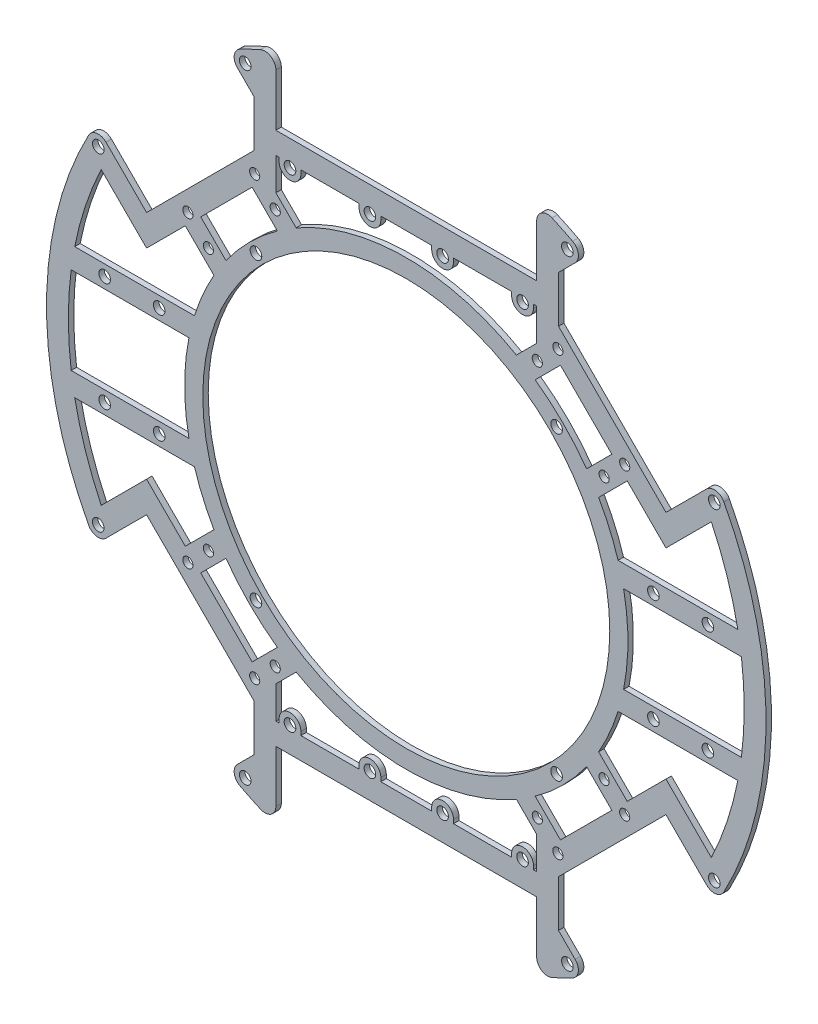
SolidWorks part; units mm, degrees
ref_plane "Front" through (0, 0, 0) normal (0, 0, 1) x (1, 0, 0)
ref_plane "Top" through (0, 0, 0) normal (0, 1, 0) x (1, 0, 0)
ref_plane "Right" through (0, 0, 0) normal (1, 0, 0) x (0, 0, -1)
sketch "Sketch1" plane through (0, 0, 0) normal (0, 0, 1) x (1, 0, 0)
  line L0 (-56.5685, 42.4264) -> (-49.621, 35.4789)
  line L4 (-35.8888, 73.4121) -> (-35.8888, 92.2659)
  line L9 (-42.4264, 56.5685) -> (-35.4789, 49.621)
  line L12 (-57.3374, 34.71) -> (-52.937, 30.3096)
  line L13 (-57.3374, 34.71) -> (-60.8112, 38.1838)
  line L16 (-41.8888, 80.4121) -> (-41.8888, 65.5914)
  line L17 (-35.8888, 67.4121) -> (-35.8888, 58.5162)
  line L19 (-41.8888, 80.4121) -> (-48.0398, 86.5631)
  line L23 (60.8112, 38.1838) -> (71.4656, 27.5293)
  line L27 (0, 67.4121) -> (-35.8888, 67.4121)
  line L28 (-53.7401, 53.7401) -> (-41.8888, 65.5914)
  line L41 (-35.8888, 58.5162) -> (-30.3096, 52.937)
  line L42 (-30.3096, 52.937) -> (-35.8888, 58.5162)
  line L45 (-53.7401, 53.7401) -> (-65.0538, 42.4264)
  line L46 (42.4264, 56.5685) -> (56.5685, 42.4264)
  line L64 (0, 0) -> (20.276, 0)
  line L79 (-42.4264, 56.5685) -> (-56.5685, 42.4264)
  line L84 (-65.0538, 42.4264) -> (-71.4656, 36.0146)
  line L85 (83.9512, 40.0149) -> (71.4656, 27.5293)
  line L90 (53.7401, 53.7401) -> (65.0538, 42.4264)
  line L91 (30.3096, 52.937) -> (35.8888, 58.5162)
  line L92 (82.6416, 47.1906) -> (71.4656, 36.0146)
  line L93 (-82.6416, 47.1906) -> (-71.4656, 36.0146)
  line L94 (-35.8888, 73.4121) -> (35.8888, 73.4121)
  line L95 (35.8888, 58.5162) -> (30.3096, 52.937)
  line L96 (53.7401, 53.7401) -> (41.8888, 65.5914)
  line L97 (41.8888, 80.4121) -> (41.8888, 65.5914)
  line L98 (0, 0) -> (0, 18.683)
  line L99 (35.8888, 67.4121) -> (35.8888, 58.5162)
  line L100 (41.8888, 80.4121) -> (48.0398, 86.5631)
  line L101 (57.3374, 34.71) -> (60.8112, 38.1838)
  line L102 (57.3374, 34.71) -> (52.937, 30.3096)
  line L104 (65.0538, 42.4264) -> (71.4656, 36.0146)
  line L105 (-83.9512, 40.0149) -> (-71.4656, 27.5293)
  line L106 (-60.8112, 38.1838) -> (-71.4656, 27.5293)
  line L107 (82.6416, -47.1906) -> (71.4656, -36.0146)
  line L108 (65.0538, -42.4264) -> (71.4656, -36.0146)
  line L109 (42.4264, 56.5685) -> (35.4789, 49.621)
  line L110 (35.8888, 73.4121) -> (35.8888, 92.2659)
  line L111 (56.5685, 42.4264) -> (49.621, 35.4789)
  line L112 (0, 67.4121) -> (35.8888, 67.4121)
  line L113 (0, -67.4121) -> (35.8888, -67.4121)
  line L114 (56.5685, -42.4264) -> (49.621, -35.4789)
  line L115 (35.8888, -73.4121) -> (35.8888, -92.2659)
  line L116 (42.4264, -56.5685) -> (35.4789, -49.621)
  line L117 (60.8112, -38.1838) -> (71.4656, -27.5293)
  line L118 (57.3374, -34.71) -> (52.937, -30.3096)
  line L119 (57.3374, -34.71) -> (60.8112, -38.1838)
  line L120 (41.8888, -80.4121) -> (48.0398, -86.5631)
  line L121 (35.8888, -67.4121) -> (35.8888, -58.5162)
  line L122 (0, 0) -> (0, -18.683)
  line L123 (41.8888, -80.4121) -> (41.8888, -65.5914)
  line L124 (53.7401, -53.7401) -> (41.8888, -65.5914)
  line L125 (35.8888, -58.5162) -> (30.3096, -52.937)
  line L126 (-35.8888, -73.4121) -> (35.8888, -73.4121)
  line L127 (30.3096, -52.937) -> (35.8888, -58.5162)
  line L128 (53.7401, -53.7401) -> (65.0538, -42.4264)
  line L129 (83.9512, -40.0149) -> (71.4656, -27.5293)
  line L130 (-82.6416, -47.1906) -> (-71.4656, -36.0146)
  line L131 (-65.0538, -42.4264) -> (-71.4656, -36.0146)
  line L132 (-42.4264, -56.5685) -> (-56.5685, -42.4264)
  line L133 (-83.9512, -40.0149) -> (-71.4656, -27.5293)
  line L134 (-60.8112, -38.1838) -> (-71.4656, -27.5293)
  line L135 (42.4264, -56.5685) -> (56.5685, -42.4264)
  line L136 (-53.7401, -53.7401) -> (-65.0538, -42.4264)
  line L137 (-30.3096, -52.937) -> (-35.8888, -58.5162)
  line L138 (-35.8888, -58.5162) -> (-30.3096, -52.937)
  line L139 (-53.7401, -53.7401) -> (-41.8888, -65.5914)
  line L140 (0, -67.4121) -> (-35.8888, -67.4121)
  line L142 (-41.8888, -80.4121) -> (-48.0398, -86.5631)
  line L143 (-35.8888, -67.4121) -> (-35.8888, -58.5162)
  line L144 (-41.8888, -80.4121) -> (-41.8888, -65.5914)
  line L146 (-57.3374, -34.71) -> (-60.8112, -38.1838)
  line L147 (-57.3374, -34.71) -> (-52.937, -30.3096)
  line L149 (-42.4264, -56.5685) -> (-35.4789, -49.621)
  line L150 (-35.8888, -73.4121) -> (-35.8888, -92.2659)
  line L151 (-56.5685, -42.4264) -> (-49.621, -35.4789)
  arc A22 (-35.8888, 92.2659) -> (-48.0398, 86.5631) centre (0, 0) ccw
  circle A24 centre (-36.0624, 54.4472) radius 1.4
  circle A25 centre (-54.4472, 36.0624) radius 1.4
  circle A26 centre (-60.1041, 41.7193) radius 1.4
  circle A27 centre (-41.7193, 60.1041) radius 1.4
  arc A31 (-52.937, 30.3096) -> (-52.937, -30.3096) centre (0, 0) ccw
  arc A36 (-35.8888, 92.2659) -> (-48.0398, 86.5631) centre (0, 0) ccw
  circle A38 centre (41.3657, 41.3657) radius 1.6
  circle A41 centre (41.7193, 60.1041) radius 1.4
  circle A42 centre (60.1041, 41.7193) radius 1.4
  circle A43 centre (54.4472, 36.0624) radius 1.4
  circle A45 centre (0, 0) radius 56
  circle A50 centre (36.0624, 54.4472) radius 1.4
  arc A55 (35.8888, 92.2659) -> (48.0398, 86.5631) centre (0, 0) cw
  circle A61 centre (-40.5714, 87.0055) radius 1.6
  circle A63 centre (40.5714, -87.0055) radius 1.6
  circle A64 centre (-40.5714, -87.0055) radius 1.6
  circle A66 centre (41.3657, 41.3657) radius 1.6
  circle A67 centre (41.3657, -41.3657) radius 1.6
  circle A69 centre (-41.3657, 41.3657) radius 1.6
  arc A73 (35.8888, -92.2659) -> (48.0398, -86.5631) centre (0, 0) ccw
  arc A74 (83.9512, -40.0149) -> (83.9512, 40.0149) centre (0, 0) ccw
  circle A75 centre (-84.763, 45.0693) radius 1.6
  arc A76 (-82.6416, 47.1906) -> (-87.4118, 46.4777) centre (-84.763, 45.0693) ccw
  arc A77 (-83.9512, 40.0149) -> (-83.9512, -40.0149) centre (0, 0) ccw
  circle A78 centre (-41.3657, -41.3657) radius 1.6 [skipped]
  arc A79 (-87.4118, 46.4777) -> (-87.4118, -46.4777) centre (0, 0) ccw
  arc A80 (82.6416, 47.1906) -> (87.4118, 46.4777) centre (84.763, 45.0693) cw
  circle A81 centre (84.763, 45.0693) radius 1.6
  circle A82 centre (40.5714, 87.0055) radius 1.6
  arc A83 (-35.4789, 49.621) -> (-49.621, 35.4789) centre (0, 0) ccw
  arc A84 (30.3096, 52.937) -> (-30.3096, 52.937) centre (0, 0) ccw
  arc A85 (49.621, 35.4789) -> (35.4789, 49.621) centre (0, 0) ccw
  arc A86 (49.621, -35.4789) -> (35.4789, -49.621) centre (0, 0) cw
  arc A87 (30.3096, -52.937) -> (-30.3096, -52.937) centre (0, 0) cw
  arc A88 (-35.4789, -49.621) -> (-49.621, -35.4789) centre (0, 0) cw
  circle A89 centre (40.5714, -87.0055) radius 1.6
  circle A90 centre (-41.3657, -41.3657) radius 1.6
  circle A91 centre (41.3657, -41.3657) radius 1.6
  circle A92 centre (-40.5714, -87.0055) radius 1.6
  arc A95 (35.8888, -92.2659) -> (48.0398, -86.5631) centre (0, 0) ccw
  arc A96 (82.6416, -47.1906) -> (87.4118, -46.4777) centre (84.763, -45.0693) ccw
  circle A97 centre (36.0624, -54.4472) radius 1.4
  circle A98 centre (54.4472, -36.0624) radius 1.4
  circle A99 centre (60.1041, -41.7193) radius 1.4
  circle A100 centre (41.7193, -60.1041) radius 1.4
  circle A102 centre (41.3657, -41.3657) radius 1.6
  circle A103 centre (-41.7193, -60.1041) radius 1.4
  circle A104 centre (-60.1041, -41.7193) radius 1.4
  circle A105 centre (-54.4472, -36.0624) radius 1.4
  circle A106 centre (-36.0624, -54.4472) radius 1.4
  circle A107 centre (84.763, -45.0693) radius 1.6
  arc A108 (-35.8888, -92.2659) -> (-48.0398, -86.5631) centre (0, 0) cw
  arc A109 (35.8888, -92.2659) -> (48.0398, -86.5631) centre (0, 0) ccw
  arc A110 (-49.621, -35.4789) -> (-35.4789, -49.621) centre (0, 0) ccw
  arc A111 (-48.0398, -86.5631) -> (-35.8888, -92.2659) centre (0, 0) ccw
  arc A112 (-30.3096, -52.937) -> (30.3096, -52.937) centre (0, 0) ccw
  arc A113 (-82.6416, -47.1906) -> (-87.4118, -46.4777) centre (-84.763, -45.0693) cw
  circle A114 centre (-84.763, -45.0693) radius 1.6
  arc A115 (35.4789, -49.621) -> (49.621, -35.4789) centre (0, 0) ccw
  arc A116 (52.937, -30.3096) -> (52.937, 30.3096) centre (0, 0) ccw
  arc A117 (-48.0398, -86.5631) -> (-35.8888, -92.2659) centre (0, 0) ccw
  arc A118 (87.4118, -46.4777) -> (87.4118, 46.4777) centre (0, 0) ccw
  arc A119 (48.0398, 86.5631) -> (35.8888, 92.2659) centre (0, 0) ccw
  dimension "D3" = 4
extrude "Boss-Extrude2" add sketch "Sketch1" along normal blind 1.5 contours A96 A118 A80 L92 L104 L90 L96 L97 L100 A55 L110 L94 L4 A76 L19 L16 L28 L45 L84 L93 A79 A113 L130 L131 L136 L139 L144 L142 A108 L150 L126 L115 A73 L120 L123 L124 L128 L108 L107 L118 A116 L102 L101 L23 L85 A74 L129 L117 L119
sketch "Sketch2" plane through (0, 0, 1.5) normal (0, 0, 1) x (1, 0, 0)
  line L0 (-41.8888, 80.4121) -> (-41.8888, 78.4121)
  line L1 (-41.8888, 80.4121) -> (-41.8888, 65.5914) construction
  line L2 (-41.8888, 78.4121) -> (-49.318, 85.8413)
  line L3 (-41.8888, 80.4121) -> (-41.8888, 84.2527)
  line L4 (-41.8888, 84.2527) -> (-45.54, 87.904)
  line L6 (41.8888, 84.2527) -> (45.54, 87.904)
  line L7 (41.8888, 80.4121) -> (41.8888, 84.2527)
  line L8 (41.8888, 78.4121) -> (49.318, 85.8413)
  line L9 (41.8888, 80.4121) -> (41.8888, 78.4121)
  line L11 (41.8888, -80.4121) -> (41.8888, -78.4121)
  line L12 (41.8888, -78.4121) -> (49.318, -85.8413)
  line L13 (41.8888, -80.4121) -> (41.8888, -84.2527)
  line L14 (41.8888, -84.2527) -> (45.54, -87.904)
  line L15 (-41.8888, -84.2527) -> (-45.54, -87.904)
  line L16 (-41.8888, -80.4121) -> (-41.8888, -84.2527)
  line L17 (-41.8888, -78.4121) -> (-49.318, -85.8413)
  line L18 (-41.8888, -80.4121) -> (-41.8888, -78.4121)
  arc A0 (-45.54, 87.904) -> (-49.318, 85.8413) centre (0, 0) ccw
  arc A1 (45.54, 87.904) -> (49.318, 85.8413) centre (0, 0) cw
  arc A2 (45.54, -87.904) -> (49.318, -85.8413) centre (0, 0) ccw
  arc A3 (-45.54, -87.904) -> (-49.318, -85.8413) centre (0, 0) cw
extrude "Boss-Extrude3" add sketch "Sketch2" against normal up to surface (1.5 mm away) up to face at (69.4302, 0, 0)
sketch "Sketch3" plane through (0, 0, 1.5) normal (0, 0, 1) x (1, 0, 0)
  circle A1 centre (-44.3279, 85.153) radius 1.6
  circle A2 centre (44.3279, 85.153) radius 1.6
  circle A3 centre (44.3279, -85.153) radius 1.6
  circle A4 centre (-44.3279, -85.153) radius 1.6
extrude "Cut-Extrude1" cut sketch "Sketch3" against normal blind 10
sketch "Sketch4" plane through (0, 0, 1.5) normal (0, 0, 1) x (1, 0, 0)
  circle A0 centre (-40.5714, 87.0055) radius 1.6
  circle A1 centre (40.5714, 87.0055) radius 1.6
  circle A2 centre (40.5714, -87.0055) radius 1.6
  circle A3 centre (-40.5714, -87.0055) radius 1.6
extrude "Boss-Extrude4" add sketch "Sketch4" against normal up to surface (1.5 mm away) up to face at (-42.7279, -85.153, 0)
fillet "Fillet1" radius 3 8 edges at (-49.318, 85.8413, 0.75) (-35.8888, 92.2659, 0.75) (35.8888, 92.2659, 0.75) (49.318, 85.8413, 0.75) (35.8888, -92.2659, 0.75) (49.318, -85.8413, 0.75) (-49.318, -85.8413, 0.75) (-35.8888, -92.2659, 0.75)
sketch "Sketch5" plane through (0, 0, 1.5) normal (0, 0, 1) x (1, 0, 0)
  line L1 (35.8888, 67.4121) -> (-35.8888, 67.4121) construction
  line L2 (-9.7752, 70.1873) -> (-13, 67.4121)
  line L3 (7, 66.4121) -> (7, 67.4121)
  line L4 (13, 66.4121) -> (13, 67.4121)
  line L5 (7, 67.4121) -> (9.7752, 70.1873)
  line L6 (9.7752, 70.1873) -> (13, 67.4121)
  line L7 (-7, 67.4121) -> (-9.7752, 70.1873)
  line L8 (-13, 66.4121) -> (-13, 67.4121)
  line L9 (-7, 66.4121) -> (-7, 67.4121)
  line L11 (-7, -66.4121) -> (-7, -67.4121)
  line L12 (-13, -66.4121) -> (-13, -67.4121)
  line L13 (-7, -67.4121) -> (-9.7752, -70.1873)
  line L14 (9.7752, -70.1873) -> (13, -67.4121)
  line L15 (7, -67.4121) -> (9.7752, -70.1873)
  line L16 (13, -66.4121) -> (13, -67.4121)
  line L17 (7, -66.4121) -> (7, -67.4121)
  line L18 (-9.7752, -70.1873) -> (-13, -67.4121)
  line L19 (0, -67.4121) -> (0, -66.4121)
  arc A0 (7, 66.4121) -> (13, 66.4121) centre (10, 66.4121) ccw
  circle A1 centre (10, 66.4121) radius 1.6
  circle A2 centre (-10, 66.4121) radius 1.6
  arc A3 (-7, 66.4121) -> (-13, 66.4121) centre (-10, 66.4121) cw
  arc A4 (-7, -66.4121) -> (-13, -66.4121) centre (-10, -66.4121) ccw
  circle A5 centre (-10, -66.4121) radius 1.6
  circle A6 centre (10, -66.4121) radius 1.6
  arc A7 (7, -66.4121) -> (13, -66.4121) centre (10, -66.4121) cw
extrude "Boss-Extrude5" add sketch "Sketch5" against normal blind 1.5 contours A3 L9 L7 L2 L8 A2 | L3 A0 L4 L6 L5 A1 | A7 L17 L15 L14 L16 A6 | L11 A4 L12 L18 L13 A5
sketch "Sketch6" plane through (0, 0, 1.5) normal (0, 0, 1) x (1, 0, 0)
  circle A0 centre (-10, -66.4121) radius 1.6
  circle A1 centre (10, -66.4121) radius 1.6
  circle A2 centre (10, 66.4121) radius 1.6
  circle A3 centre (-10, 66.4121) radius 1.6
extrude "Cut-Extrude2" cut sketch "Sketch6" against normal blind 1.5
sketch "Sketch9" plane through (0, 0, 1.5) normal (0, 0, 1) x (1, 0, 0)
  line L1 (-35, 66.4121) -> (-35, 67.4121)
  line L2 (-13, 67.4121) -> (-35.8888, 67.4121) construction
  line L3 (-29, 66.4121) -> (-29, 67.4121)
  line L4 (-29, 67.4121) -> (-35, 67.4121)
  line L6 (29, 67.4121) -> (35, 67.4121)
  line L7 (29, 66.4121) -> (29, 67.4121)
  line L8 (35, 66.4121) -> (35, 67.4121)
  line L9 (35, -66.4121) -> (35, -67.4121)
  line L10 (29, -66.4121) -> (29, -67.4121)
  line L11 (29, -67.4121) -> (35, -67.4121)
  line L12 (-29, -67.4121) -> (-35, -67.4121)
  line L13 (-29, -66.4121) -> (-29, -67.4121)
  line L14 (-35, -66.4121) -> (-35, -67.4121)
  arc A0 (-35, 66.4121) -> (-29, 66.4121) centre (-32, 66.4121) ccw
  arc A1 (-33.249, 67.4121) -> (-30.751, 67.4121) centre (-32, 66.4121) ccw
  arc A2 (33.249, 67.4121) -> (30.751, 67.4121) centre (32, 66.4121) cw
  arc A3 (35, 66.4121) -> (29, 66.4121) centre (32, 66.4121) cw
  arc A4 (35, -66.4121) -> (29, -66.4121) centre (32, -66.4121) ccw
  arc A5 (33.249, -67.4121) -> (30.751, -67.4121) centre (32, -66.4121) ccw
  arc A6 (-33.249, -67.4121) -> (-30.751, -67.4121) centre (-32, -66.4121) cw
  arc A7 (-35, -66.4121) -> (-29, -66.4121) centre (-32, -66.4121) cw
extrude "Boss-Extrude7" add sketch "Sketch9" against normal blind 1.5 contours A3 L8 L6 A2 L7 | A1 L4 L1 A0 L3 | A7 L14 L12 A6 L13 | A5 L11 L9 A4 L10
sketch "Sketch10" plane through (0, 0, 1.5) normal (0, 0, 1) x (1, 0, 0)
  circle A0 centre (-32, 66.4121) radius 1.6
  circle A1 centre (32, 66.4121) radius 1.6
  circle A2 centre (32, -66.4121) radius 1.6
  circle A3 centre (-32, -66.4121) radius 1.6
extrude "Cut-Extrude3" cut sketch "Sketch10" against normal blind 1.5
sketch "Sketch11" plane through (0, 0, 1.5) normal (0, 0, 1) x (1, 0, 0)
  line L1 (-93, 12) -> (-93, 15)
  line L2 (-93, -18) -> (-91.2414, -18)
  line L3 (-93, -12) -> (-93, -18)
  line L4 (-56.4938, -12) -> (-93, -12)
  line L5 (-83, 18) -> (-56.4938, 18)
  line L6 (-83, 18) -> (-91.2414, 18)
  line L7 (-56.4938, 18) -> (-56.4938, 12)
  line L8 (-56.4938, 12) -> (-93, 12)
  line L9 (-93, 12) -> (-93, 18)
  line L10 (-93, 18) -> (-91.2414, 18)
  line L11 (-56.4938, -18) -> (-56.4938, -12)
  line L12 (-83, -18) -> (-91.2414, -18)
  line L13 (-83, -18) -> (-56.4938, -18)
  line L14 (-93, -12) -> (-93, -15)
  line L15 (93, -12) -> (93, -15)
  line L16 (83, -18) -> (56.4938, -18)
  line L17 (83, -18) -> (91.2414, -18)
  line L18 (56.4938, -18) -> (56.4938, -12)
  line L19 (93, 18) -> (91.2414, 18)
  line L20 (93, 12) -> (93, 18)
  line L21 (56.4938, 12) -> (93, 12)
  line L22 (56.4938, 18) -> (56.4938, 12)
  line L23 (83, 18) -> (91.2414, 18)
  line L24 (83, 18) -> (56.4938, 18)
  line L25 (56.4938, -12) -> (93, -12)
  line L26 (93, -12) -> (93, -18)
  line L27 (93, -18) -> (91.2414, -18)
  line L28 (93, 12) -> (93, 15)
  arc A0 (-83.9512, 40.0149) -> (-83.9512, -40.0149) centre (0, 0) ccw construction
  circle A1 centre (-83, 15) radius 1.6
  circle A2 centre (-68, 15) radius 1.6
  circle A3 centre (-68, -15) radius 1.6
  circle A4 centre (-83, -15) radius 1.6
  circle A5 centre (83, -15) radius 1.6
  circle A6 centre (68, -15) radius 1.6
  circle A7 centre (68, 15) radius 1.6
  circle A8 centre (83, 15) radius 1.6
extrude "Boss-Extrude8" add sketch "Sketch11" against normal blind 1.5 contours L10 L9 L1 L8 L7 L5 L6 A2 A1 | L12 L13 L11 L4 L3 L2 A3 A4 | L23 L24 L22 L21 L20 L19 A7 A8 | L27 L26 L15 L25 L18 L16 L17 A6 A5
